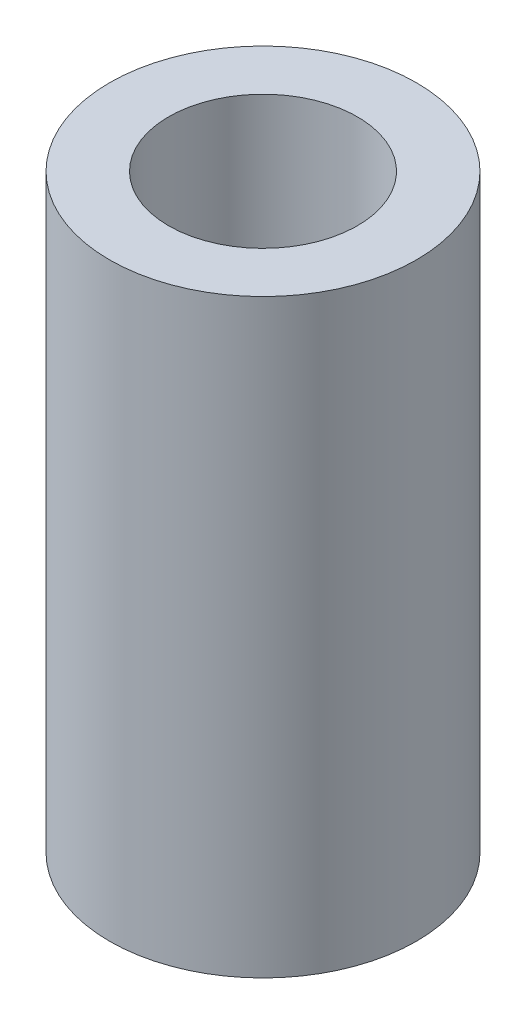
SolidWorks part; units mm, degrees
ref_plane "Front Plane" through (0, 0, 0) normal (0, 0, 1) x (1, 0, 0)
ref_plane "Top Plane" through (0, 0, 0) normal (0, 1, 0) x (1, 0, 0)
ref_plane "Right Plane" through (0, 0, 0) normal (1, 0, 0) x (0, 0, -1)
sketch "Sketch1" plane through (0, 0, 0) normal (0, 1, 0) x (1, 0, 0)
  circle A0 centre (0, 0) radius 1.6
  circle A1 centre (0, 0) radius 2.6
  dimension "D1" = 3.2
  dimension "D2" = 1
extrude "Boss-Extrude1" add sketch "Sketch1" along normal blind 10
